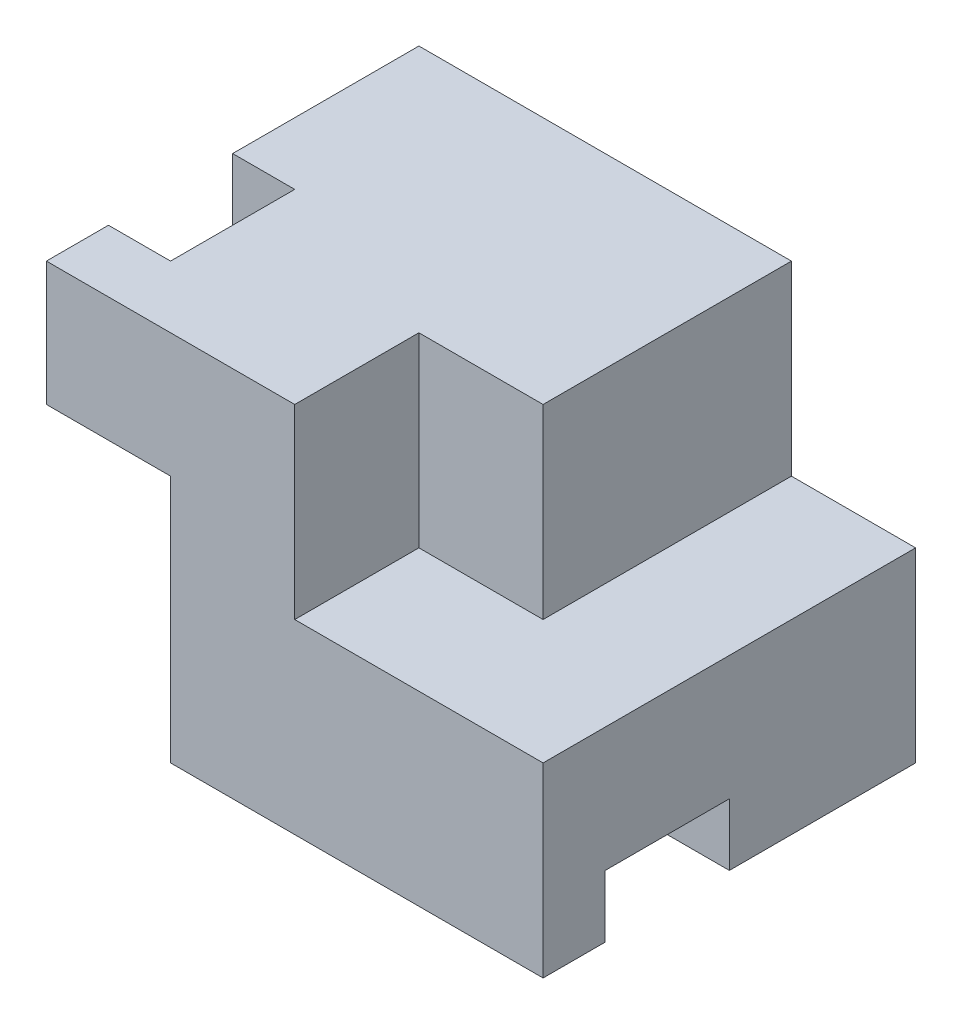
SolidWorks part; units mm, degrees
ref_plane "Front Plane" through (0, 0, 0) normal (0, 0, 1) x (1, 0, 0)
ref_plane "Top Plane" through (0, 0, 0) normal (0, 1, 0) x (1, 0, 0)
ref_plane "Right Plane" through (0, 0, 0) normal (1, 0, 0) x (0, 0, -1)
sketch "Sketch2" plane through (0, 0, 0) normal (0, 0, 1) x (1, 0, 0)
  line L1 (0, 0) -> (203.2, 0)
  line L2 (0, 0) -> (0, 152.4)
  line L3 (0, 152.4) -> (203.2, 152.4)
  line L4 (203.2, 0) -> (203.2, 152.4)
  dimension "D1" = 203.2
  dimension "D2" = 152.4
extrude "Boss-Extrude1" add sketch "Sketch2" against normal blind 152.4
sketch "Sketch4" plane through (0, 0, 0) normal (0, 0, 1) x (1, 0, 0)
  line L1 (0, 0) -> (50.8, 0)
  line L2 (0, 0) -> (0, 101.6)
  line L3 (0, 101.6) -> (50.8, 101.6)
  line L4 (50.8, 0) -> (50.8, 101.6)
  dimension "D1" = 50.8
  dimension "D2" = 101.6
extrude "Cut-Extrude1" cut sketch "Sketch4" against normal blind 76.2
sketch "Sketch5" plane through (0, 152.4, 0) normal (0, 1, 0) x (1, 0, 0)
  line L0 (0, 152.4) -> (0, 0) construction
  line L1 (0, 25.4) -> (25.4, 25.4)
  line L2 (0, 25.4) -> (0, 76.2)
  line L3 (0, 76.2) -> (25.4, 76.2)
  line L4 (25.4, 25.4) -> (25.4, 76.2)
  line L5 (203.2, 0) -> (0, 0) construction
  dimension "D1" = 25.4
  dimension "D2" = 50.8
  dimension "D3" = 25.4
extrude "Cut-Extrude2" cut sketch "Sketch5" against normal blind 76.2
sketch "Sketch6" plane through (203.2, 0, 0) normal (1, 0, 0) x (0, 0, -1)
  line L0 (152.4, 0) -> (0, 0) construction
  line L1 (25.4, 0) -> (76.2, 0)
  line L2 (25.4, 0) -> (25.4, 25.4)
  line L3 (25.4, 25.4) -> (76.2, 25.4)
  line L4 (76.2, 0) -> (76.2, 25.4)
  line L5 (0, 0) -> (0, 152.4) construction
  dimension "D1" = 25.4
  dimension "D2" = 50.8
  dimension "D3" = 25.4
extrude "Cut-Extrude3" cut sketch "Sketch6" against normal blind 152.4
sketch "Sketch7" plane through (0, 152.4, 0) normal (0, 1, 0) x (1, 0, 0)
  line L0 (152.4, 152.4) -> (152.4, 50.8)
  line L1 (203.2, 152.4) -> (0, 152.4) construction
  line L2 (152.4, 50.8) -> (101.6, 50.8)
  line L3 (101.6, 50.8) -> (101.6, 0)
  line L4 (203.2, 0) -> (0, 0) construction
  line L5 (101.6, 0) -> (203.2, 0)
  line L6 (203.2, 0) -> (203.2, 152.4)
  line L7 (203.2, 152.4) -> (152.4, 152.4)
  dimension "D1" = 50.8
  dimension "D2" = 101.6
  dimension "D3" = 101.6
  dimension "D4" = 50.8
extrude "Cut-Extrude4" cut sketch "Sketch7" against normal blind 76.2
